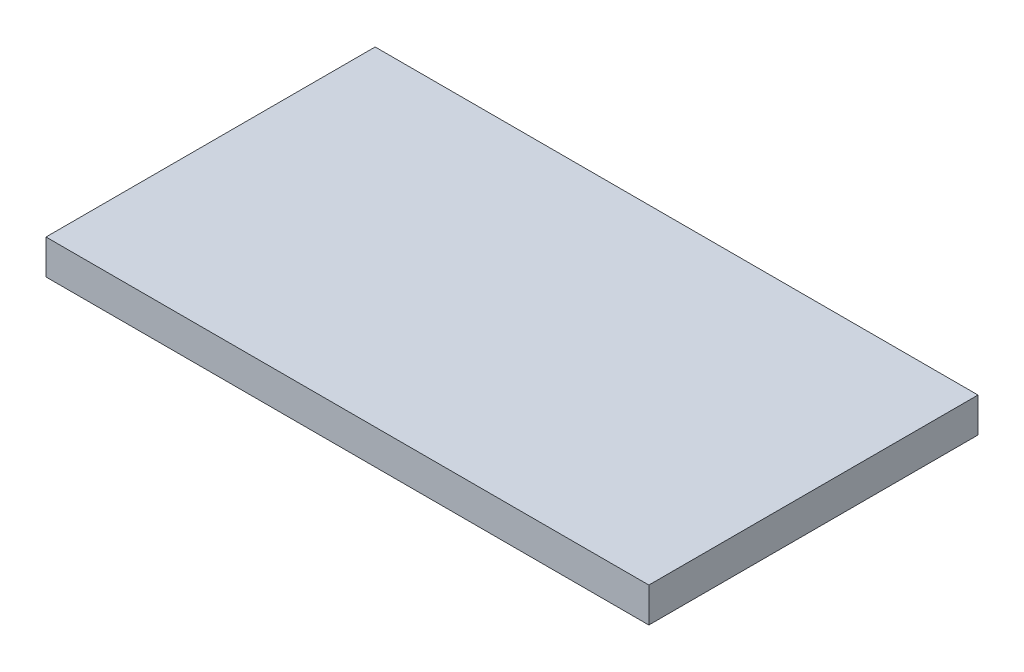
SolidWorks part; units mm, degrees
material "Custom Plastic"
ref_plane "Front Plane" through (0, 0, 0) normal (0, 0, 1) x (1, 0, 0)
ref_plane "Top Plane" through (0, 0, 0) normal (0, 1, 0) x (1, 0, 0)
ref_plane "Right Plane" through (0, 0, 0) normal (1, 0, 0) x (0, 0, -1)
sketch "Sketch1" plane through (0, 0, 0) normal (0, 1, 0) x (1, 0, 0)
  line L0 (-35.9391, 2.55) -> (38.4915, 2.55) construction
  line L1 (-26.1, -11.7) -> (26.1, -11.7)
  line L2 (-26.1, -11.7) -> (-26.1, 16.8)
  line L3 (-26.1, 16.8) -> (26.1, 16.8)
  line L4 (26.1, -11.7) -> (26.1, 16.8)
  line L5 (-26.1, -11.7) -> (26.1, 16.8) construction
  line L6 (-26.1, 16.8) -> (26.1, -11.7) construction
  line L7 (0, 29.6091) -> (0, -31.2199) construction
  line L8 (0, 16.8) -> (0, 0) construction
  line L10 (-17.6603, -1.9) -> (17.6603, -1.9)
  line L11 (-17.6603, 7) -> (17.6603, 7)
  line L12 (-17.6603, 7) -> (-17.6603, 12.8)
  line L13 (-17.6603, 12.8) -> (17.6603, 12.8)
  line L14 (17.6603, 7) -> (17.6603, 12.8)
  line L23 (17.6603, -1.9) -> (17.6603, -7.7)
  line L24 (-17.6603, -7.7) -> (17.6603, -7.7)
  line L25 (-17.6603, -1.9) -> (-17.6603, -7.7)
  circle A0 centre (-22.8, -3.2) radius 1
  circle A1 centre (22.8, -3.2) radius 1
  circle A2 centre (22.8, 8.3) radius 1
  circle A3 centre (-22.8, 8.3) radius 1
  point P0 (0, 0)
  dimension "D3" = 2
  dimension "D1" = 28.5
  dimension "D2" = 52.2
  dimension "D4" = 8.5
  dimension "D5" = 8.5
  dimension "D7" = 4
  dimension "D9" = 5.8
  dimension "D10" = 35.3206
  dimension "D11" = 8.4397
extrude "Boss-Extrude1" add sketch "Sketch1" along normal blind 2.5
sketch "Sketch2" plane through (0, 0, 0) normal (0, -1, 0) x (1, 0, 0)
  line L1 (-26.1, 11.7) -> (-26.1, -16.8)
  line L2 (-26.1, 11.7) -> (26.1, 11.7) construction
  line L3 (-26.1, -16.8) -> (26.1, -16.8)
  line L4 (26.1, -16.8) -> (26.1, 11.7)
  line L5 (26.1, 11.7) -> (-26.1, 11.7)
extrude "Boss-Extrude2" add sketch "Sketch2" against normal blind 3
